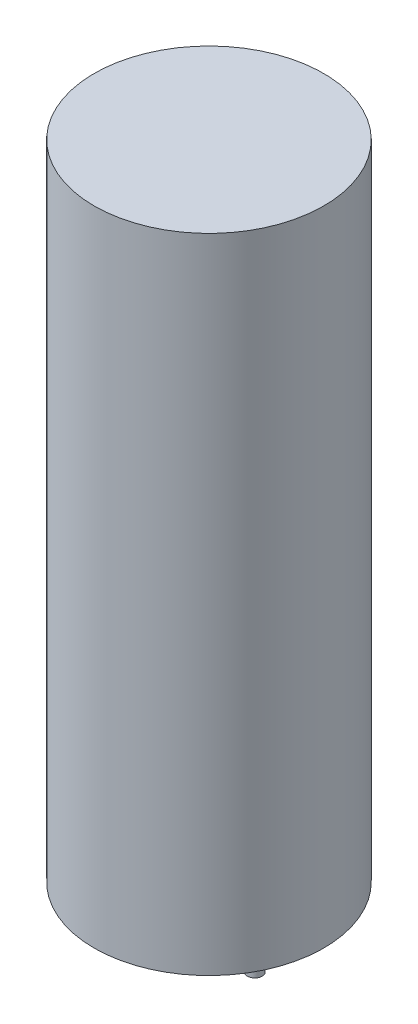
SolidWorks part; units mm, degrees
ref_plane "前视基准面" through (0, 0, 0) normal (0, 0, 1) x (1, 0, 0)
ref_plane "上视基准面" through (0, 0, 0) normal (0, 1, 0) x (1, 0, 0)
ref_plane "右视基准面" through (0, 0, 0) normal (1, 0, 0) x (0, 0, -1)
sketch "草图1" plane through (0, 0, 0) normal (0, 1, 0) x (1, 0, 0)
  circle A2 centre (-2.5, 0) radius 0.4
  circle A3 centre (2.5, 0) radius 0.4
  circle A4 centre (0, 0) radius 6.25
  point P2 (0, 0)
extrude "凸台-拉伸2" add sketch "草图1" against normal blind 3 contours A2
sketch "草图2" plane through (0, 0, 0) normal (0, 1, 0) x (1, 0, 0)
  circle A0 centre (2.5, 0) radius 0.4
extrude "凸台-拉伸3" add sketch "草图2" against normal blind 3 separate body contours A0
sketch "草图3" plane through (0, 0, 0) normal (0, 1, 0) x (1, 0, 0)
  circle A0 centre (0, 0) radius 6.25
extrude "凸台-拉伸4" add sketch "草图3" along normal blind 35 contours A0
